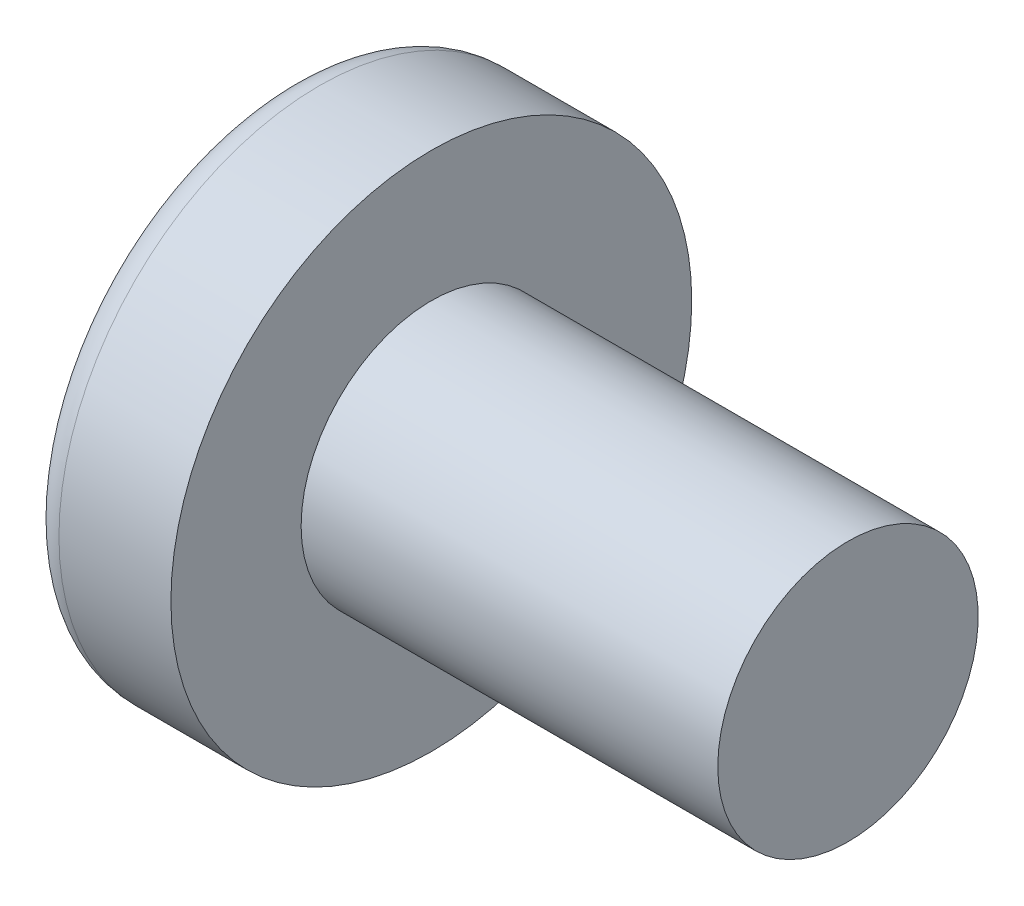
SolidWorks part; units mm, degrees
ref_plane "Plane1" through (0, 0, 0) normal (0, 0, 1) x (1, 0, 0)
ref_plane "Plane2" through (0, 0, 0) normal (0, 1, 0) x (1, 0, 0)
ref_plane "Plane3" through (0, 0, 0) normal (1, 0, 0) x (0, 0, -1)
sketch "BodySke" plane through (0, 0, 0) normal (0, 0, 1) x (1, 0, 0)
  line L0 (2.1, 1.25) -> (2.1, 2.5)
  line L1 (2.55, 6.35) -> (2.55, -3.175) construction
  line L2 (-25.4, 0) -> (127, 0) construction
  line L3 (6.1, 0) -> (0, 0)
  line L4 (2.1, 1.25) -> (6.1, 1.25)
  line L5 (6.1, 1.25) -> (6.1, 0)
  line L6 (1.0251, 2.5) -> (2.1, 2.5)
  line L7 (2.1, -1.25) -> (6.1, -1.25) construction
  line L8 (2.1, 6.35) -> (2.1, -3.175) construction
  arc A0 (0.7839, 2.3784) -> (0, 0) centre (4, 0) ccw
  arc A2 (0.7839, 2.3784) -> (1.0251, 2.5) centre (1.0251, 2.2) cw
  dimension "Head_crown_rad" = 4
  dimension "Head_fillet_rad" = 0.3
  dimension "Diameter" = 2.5
  dimension "Length" = 4
  dimension "Head_ht" = 2.1
  dimension "Head_dia" = 5
  dimension "Advance" = 0.45
  dimension "Thread_nom" = 4
revolve "Base-Revolve" add sketch "BodySke" angle 360 about L2
cosmetic thread "ThreadCosmetic" [suppressed] parameters "Thread_length"=3.55, "Thread_minor"=1.993
sketch "Sketch3" plane through (0, 0, 0) normal (1, 0, 0) x (0, 0, -1)
  line L0 (0.35, -1.34) -> (-0.35, -1.34)
  line L1 (0.35, -1.34) -> (0.35, 1.34)
  line L2 (-0.35, 1.34) -> (0.35, 1.34)
  line L3 (-0.35, 1.34) -> (-0.35, -1.34)
  dimension "Cross_dia" = 2.68
  dimension "D1" = 1.34
  dimension "Cross_width" = 0.7
  dimension "D2" = 0.35
ref_plane "Plane4" through (1.53, 0, 0) normal (1, 0, 0) x (0, 0, -1)
sketch "Sketch4" plane through (1.53, 0, 0) normal (1, 0, 0) x (0, 0, -1)
  line L0 (0.175, -0.175) -> (-0.175, -0.175)
  line L1 (0.175, -0.175) -> (0.175, 0.175)
  line L2 (-0.175, 0.175) -> (0.175, 0.175)
  line L3 (-0.175, 0.175) -> (-0.175, -0.175)
  dimension "D2" = 0.35
  dimension "D1" = 0.35
  dimension "D3" = 0.175
  dimension "D4" = 0.175
loft "Cut-Loft1" cut profiles "Sketch3", "Sketch4"
pattern_circular "CirPattern1" count 2 every 90 about axis through (0, 0, 0) along (1, 0, 0) of "Cut-Loft1"
sketch "ThdSchSke" plane through (0, 0, 0) normal (0, 0, 1) x (1, 0, 0)
  line L0 (2.55, -0.9965) -> (2.3725, -1.25)
  line L1 (2.55, -0.9965) -> (2.7275, -1.25)
  line L2 (2.7275, -1.25) -> (2.7275, -1.5625)
  line L3 (-3.175, 0) -> (5.1513, 0) construction
  line L5 (2.7275, -1.5625) -> (2.3725, -1.5625)
  line L6 (2.3725, -1.5625) -> (2.3725, -1.25)
  dimension "Diameter" = 2.5
  dimension "SideAngle" = 55
  dimension "VeeAngle" = 70
  dimension "Thread_minor" = 1.993
  dimension "Overcut" = 3.125
  dimension "Start" = 2.55
revolve "ThreadSchematic" [suppressed] cut sketch "ThdSchSke" angle 360 about L3
pattern_linear "ThdSchPat" [suppressed]
equation "\"D1@Sketch3\" = \"Cross_dia@Sketch3\" / 2"
equation "\"D2@Sketch3\" = \"Cross_width@Sketch3\" / 2"
equation "\"D1@Sketch4\" = \"Cross_width@Sketch3\" *.5"
equation "\"D2@Sketch4\" = \"D1@Sketch4\""
equation "\"D3@Sketch4\" = \"D1@Sketch4\" / 2"
equation "\"D4@Sketch4\" = \"D2@Sketch4\" / 2"
equation "\"Thread_length@ThreadCosmetic\" = ((sgn( (\"Length@BodySke\" - \"Advance@BodySke\" ) - \"Thread_nom@BodySke\" )-1)*( (\"Length@BodySke\" - \"Advance@BodySke\" ) - \"Thread_nom@BodySke\" ))/-2+ \"Thread_nom@BodySke\""
equation "\"Thread_minor@ThdSchSke\" = \"Thread_minor@ThreadCosmetic\""
equation "\"Diameter@ThdSchSke\" = \"Diameter@BodySke\""
equation "\"Overcut@ThdSchSke\" = \"Diameter@BodySke\" * 1.25"
equation "\"Start@ThdSchSke\" = \"Head_ht@BodySke\" + \"Length@BodySke\" - \"Thread_length@ThreadCosmetic\"  '---Non-countersunk---"
equation "\"Num_threads@ThdSchPat\" = int( \"Thread_length@ThreadCosmetic\" / \"Advance@BodySke\" + 0.999 )  + 1"
equation "\"Advance@ThdSchPat\" = \"Thread_length@ThreadCosmetic\" /  (\"Num_threads@ThdSchPat\" - 1) 'relax it"
